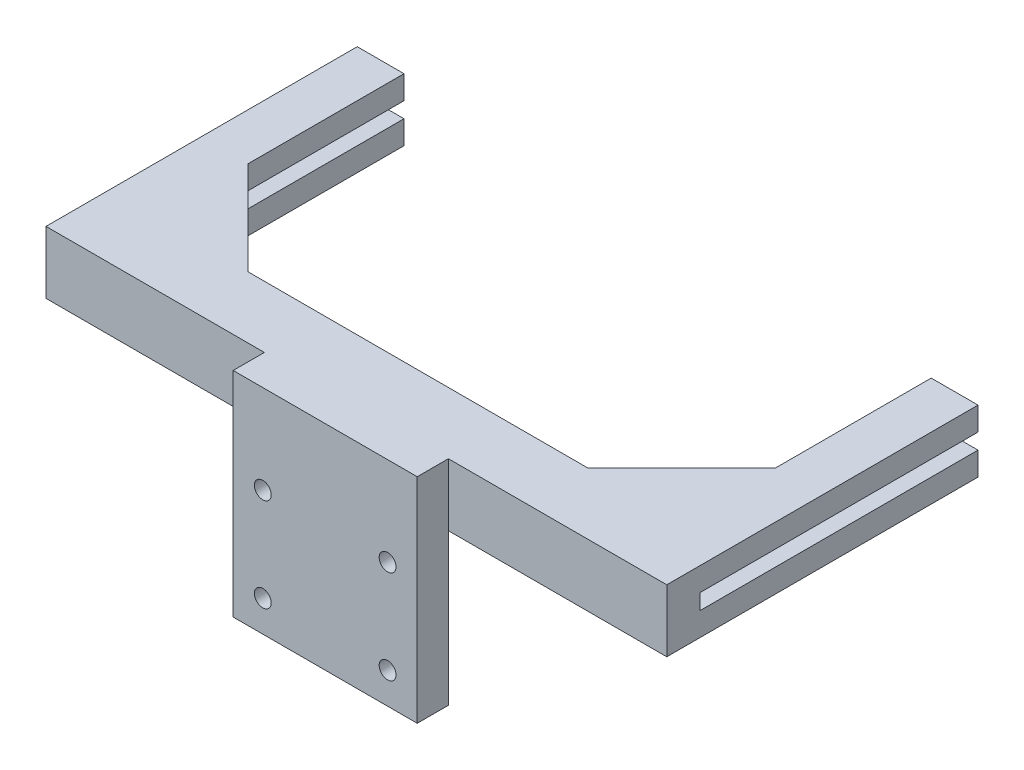
SolidWorks part; units mm, degrees
ref_plane "Front Plane" through (0, 0, 0) normal (0, 0, 1) x (1, 0, 0)
ref_plane "Top Plane" through (0, 0, 0) normal (0, 1, 0) x (1, 0, 0)
ref_plane "Right Plane" through (0, 0, 0) normal (1, 0, 0) x (0, 0, -1)
sketch "Sketch1" plane through (0, 0, 0) normal (0, 0, 1) x (1, 0, 0)
  line L1 (-29.5, -25) -> (29.5, -25)
  line L2 (-29.5, -25) -> (-29.5, 25)
  line L3 (-29.5, 25) -> (29.5, 25)
  line L4 (29.5, -25) -> (29.5, 25)
  line L5 (-29.5, -25) -> (29.5, 25) construction
  line L6 (-29.5, 25) -> (29.5, -25) construction
  point P0 (0, 0)
  dimension "D1" = 59
  dimension "D2" = 50
extrude "Boss-Extrude1" add sketch "Sketch1" along normal blind 10
sketch "Sketch2" plane through (0, 0, 10) normal (0, 0, 1) x (1, 0, 0)
  line L0 (0, -33) -> (0, 33) construction
  line L1 (77, 0) -> (-77, 0) construction
  circle A0 centre (-20, 15) radius 2.7
  dimension "D1" = 20
  dimension "D3" = 5.4
  dimension "D2" = 15
extrude "Cut-Extrude1" cut sketch "Sketch2" against normal up to surface (10 mm away) up to face at (0, 0, 0)
mirror "Mirror1" about plane through (0, 0, 0) normal (0, 1, 0) of "Cut-Extrude1" second plane through (0, 0, 0) second plane normal (1, 0, 0)
sketch "Sketch4" plane through (0, 0, 0) normal (0, 0, -1) x (-1, 0, 0)
  line L0 (-29.5, -19.3218) -> (29.5, -19.3218)
  line L1 (-29.5, -25) -> (-29.5, 25) construction
  line L2 (29.5, 25) -> (29.5, -25) construction
  line L3 (29.5, -19.3218) -> (29.5, -25)
  line L4 (29.5, -25) -> (-29.5, -25)
  line L5 (-29.5, -25) -> (-29.5, -19.3218)
sketch "Sketch9" plane through (0, 25, 0) normal (0, 1, 0) x (1, 0, 0)
  line L0 (-29.5, 0) -> (29.5, 0)
  line L1 (-29.5, 0) -> (29.5, 0) construction
  line L2 (-33, 0) -> (33, 0) construction
  line L3 (29.5, -10) -> (29.5, 0) construction
  line L4 (29.5, 0) -> (29.5, -10)
  line L5 (29.5, -10) -> (-29.5, -10)
  line L6 (29.5, -10) -> (-29.5, -10) construction
  line L7 (-29.5, -10) -> (-29.5, 0)
  point P8 (0, 0)
  point P14 (0, 0)
  point P15 (0, 0)
  point P16 (0, 0)
extrude "Boss-Extrude10" add sketch "Sketch9" along normal blind 18.4614
sketch "Sketch12" plane through (0, 0, 0) normal (0, 0, -1) x (-1, 0, 0)
  line L0 (-29.5, 43.4614) -> (29.5, 43.4614)
  line L1 (29.5, 43.4614) -> (29.5, 23.4614)
  line L2 (29.5, 43.4614) -> (29.5, -25) construction
  line L3 (29.5, 23.4614) -> (-29.5, 23.4614)
  line L4 (-29.5, -25) -> (-29.5, 43.4614) construction
  line L5 (-29.5, 23.4614) -> (-29.5, 43.4614)
  dimension "D1" = 20
extrude "Boss-Extrude11" add sketch "Sketch12" along normal blind 19.7701
sketch "Sketch13" plane through (-29.5, 0, 0) normal (-1, 0, 0) x (0, 0, 1)
  line L0 (-19.7701, 43.4614) -> (0, 43.4614)
  line L1 (0, -36.6463) -> (0, 36.6463) construction
  line L2 (-19.7701, 43.4614) -> (10, 43.4614) construction
  line L3 (0, 43.4614) -> (0, 23.4614)
  line L4 (-19.7701, 23.4614) -> (0, 23.4614) construction
  line L5 (0, 23.4614) -> (-19.7701, 23.4614)
  line L6 (-19.7701, 23.4614) -> (-19.7701, 43.4614)
  point P12 (0, 25)
  point P13 (0, 35)
extrude "Boss-Extrude12" add sketch "Sketch13" along normal blind 70
sketch "Sketch14" plane through (0, 0, -19.7701) normal (0, 0, -1) x (-1, 0, 0)
  line L0 (84.5, 43.4614) -> (99.5, 43.4614)
  line L1 (99.5, 43.4614) -> (-29.5, 43.4614) construction
  line L2 (99.5, 43.4614) -> (99.5, 23.4614)
  line L3 (99.5, 23.4614) -> (84.5, 23.4614)
  line L4 (-29.5, 23.4614) -> (99.5, 23.4614) construction
  line L5 (84.5, 23.4614) -> (84.5, 43.4614)
  dimension "D1" = 15
extrude "Boss-Extrude13" add sketch "Sketch14" along normal blind 80
mirror "Mirror2" about plane through (0, 0, 0) normal (1, 0, 0) of "Boss-Extrude13", "Boss-Extrude12"
sketch "Sketch15" plane through (0, 43.4614, 0) normal (0, 1, 0) x (1, 0, 0)
  line L0 (-84.5, 19.7701) -> (-54.5, 19.7701)
  line L1 (-84.5, 19.7701) -> (84.5, 19.7701) construction
  line L2 (-54.5, 19.7701) -> (-84.5, 49.7701)
  line L3 (-84.5, 99.7701) -> (-84.5, 19.7701) construction
  line L4 (-84.5, 49.7701) -> (-84.5, 19.7701)
  dimension "D1" = 30
  dimension "D2" = 30
extrude "Boss-Extrude14" add sketch "Sketch15" against normal up to surface (20 mm away) up to face at (0, 23.4614, -43.8621)
ref_plane "Plane1" through (0, 0, -120) normal (0, 0, 1) x (1, 0, 0)
sketch "Sketch16" plane through (0, 0, -120) normal (0, 0, 1) x (1, 0, 0)
  line L0 (99.5, 35.9614) -> (99.5, 30.9614)
  line L1 (99.5, 23.4614) -> (99.5, 43.4614) construction
  line L2 (99.5, 30.9614) -> (-99.5, 30.9614)
  line L3 (-99.5, 23.4614) -> (-99.5, 43.4614) construction
  line L4 (-99.5, 30.9614) -> (-99.5, 35.9614)
  line L5 (-99.5, 35.9614) -> (99.5, 35.9614)
  line L6 (-99.5, 43.4614) -> (-84.5, 43.4614) construction
  dimension "D1" = 5
  dimension "D2" = 7.5
mirror "Mirror3" about plane through (0, 0, 0) normal (1, 0, 0) of "Boss-Extrude14"
ref_plane "Plane2" through (10, 0, 0) normal (1, 0, 0) x (0, 0, -1)
sketch "Sketch19" plane through (10, 0, 0) normal (1, 0, 0) x (0, 0, -1)
  line L0 (0, -25) -> (19.7701, 23.4614)
  line L1 (0, -25) -> (0, -19.3218) construction
  line L2 (0, 37.6538) -> (0, -37.6538) construction
  line L3 (99.7701, 23.4614) -> (0, 23.4614) construction
  line L4 (19.7701, 23.4614) -> (0, 23.4614)
  line L5 (0, 23.4614) -> (0, -25)
  point P8 (0, 0)
  point P10 (12.4525, 25)
  point P11 (19.8544, 25)
  point P14 (0, 0)
extrude "Boss-Extrude15" add sketch "Sketch19" against normal blind 5
mirror "Mirror4" about plane through (0, 0, 0) normal (1, 0, 0) of "Boss-Extrude15"
extrude "Cut-Extrude3" cut sketch "Sketch16" along normal blind 109.3501 contours L5 L0 L2 L4
